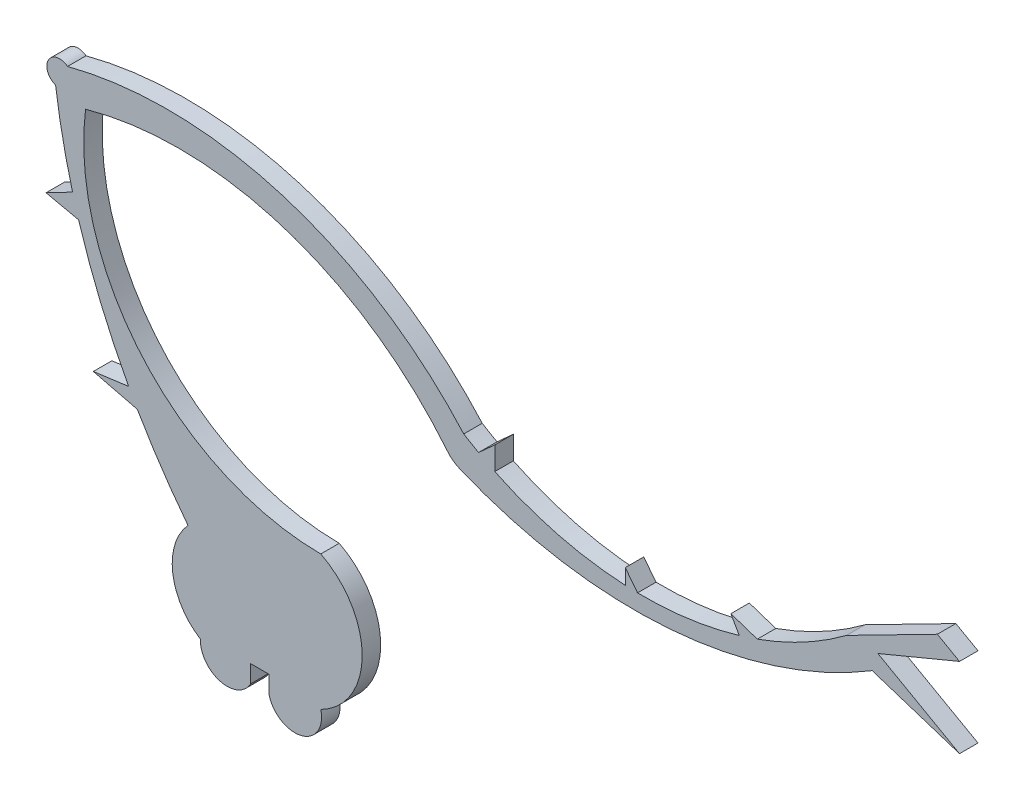
SolidWorks part; units mm, degrees
ref_plane "Front Plane" through (0, 0, 0) normal (0, 0, 1) x (1, 0, 0)
ref_plane "Top Plane" through (0, 0, 0) normal (0, 1, 0) x (1, 0, 0)
ref_plane "Right Plane" through (0, 0, 0) normal (1, 0, 0) x (0, 0, -1)
sketch "Sketch1" plane through (0, 0, 0) normal (0, 0, 1) x (1, 0, 0)
  line L0 (0, 6.0179) -> (0, 4.5667)
  line L2 (-1.524, 6.0179) -> (-1.524, 4.5667)
  line L3 (0, 4.5667) -> (0, 6.0179)
  line L5 (49.7127, 31.1308) -> (56.9103, 28.8042)
  line L6 (56.9103, 28.8042) -> (50.1851, 32.592)
  line L7 (50.1851, 32.592) -> (56.9103, 35.3889)
  line L8 (56.9103, 35.3889) -> (55.0837, 36.4177)
  line L9 (55.0837, 36.4177) -> (47.5988, 32.592)
  line L10 (40.2439, 28.6481) -> (38.0634, 29.3759)
  line L11 (38.0634, 29.3759) -> (38.7593, 28.1639)
  line L12 (29.3602, 27.048) -> (29.3602, 28.3129)
  line L13 (29.3602, 28.3129) -> (30.372, 27.0145)
  line L14 (17.2695, 30.483) -> (18.6099, 31.6968)
  line L15 (18.6099, 31.6968) -> (18.6099, 29.7926)
  line L16 (-10.856, 19.5002) -> (-14.4858, 20.3898)
  line L17 (-14.4858, 20.3898) -> (-11.5726, 20.781)
  line L18 (-15.6969, 30.6082) -> (-18.3847, 31.1954)
  line L19 (-18.3847, 31.1954) -> (-16.1971, 32.3375)
  line L20 (0, 6.0179) -> (-1.524, 6.0179)
  arc A0 (0, 4.5667) -> (4.2631, 5.6367) centre (2.1315, 5.1017) ccw
  arc A1 (-1.524, 4.5667) -> (-5.6651, 5.7011) centre (-3.4568, 5.6367) cw
  arc A2 (-5.6651, 5.7011) -> (-6.6806, 13.3064) centre (-2.9598, 9.9328) cw
  arc A3 (-6.6806, 13.3064) -> (-10.856, 19.5002) centre (35.7756, 46.4314) cw
  arc A4 (-17.5968, 39.2767) -> (-16.6105, 41.0997) centre (-17.2614, 40.2736) cw
  arc A5 (-16.6105, 41.0997) -> (16.0471, 31.1954) centre (-8.3638, 9.4984) cw
  arc A6 (16.0471, 31.1954) -> (17.2695, 30.483) centre (30.7959, 55.0976) ccw
  arc A7 (4.2631, 5.6367) -> (4.2631, 16.737) centre (1.458, 11.1868) ccw
  arc A8 (4.2631, 16.737) -> (-15.124, 38.7923) centre (4.332, 36.346) cw
  arc A9 (-15.124, 38.7923) -> (14.7104, 29.2889) centre (-7.4336, 11.3535) cw
  arc A10 (15.709, 28.5422) -> (49.7127, 31.1308) centre (30.163, 63.3044) ccw
  arc A11 (40.2439, 28.6481) -> (47.5988, 32.592) centre (30.7959, 55.0976) ccw
  arc A12 (30.372, 27.0145) -> (38.7593, 28.1639) centre (30.7959, 55.0976) ccw
  arc A13 (18.6099, 29.7926) -> (29.3602, 27.048) centre (30.7959, 55.0976) ccw
  arc A14 (14.7104, 29.2889) -> (15.709, 28.5422) centre (16.6842, 30.8875) ccw
  arc A15 (-11.5726, 20.781) -> (-15.6969, 30.6082) centre (35.7756, 46.4314) cw
  arc A16 (-16.1971, 32.3375) -> (-17.5968, 39.2767) centre (35.7756, 46.4314) cw
  dimension "D1" = 2.54
extrude "Boss-Extrude1" add sketch "Sketch1" along normal blind 1.524 contours A16 L19 L18 A15 L17 L16 A3 A2 A1 L2 L20 L0 A0 A7 A8 A9 A14 A10 L5 L6 L7 L8 L9 A11 L10 L11 A12 L13 L12 A13 L15 L14 A6 A5 A4
